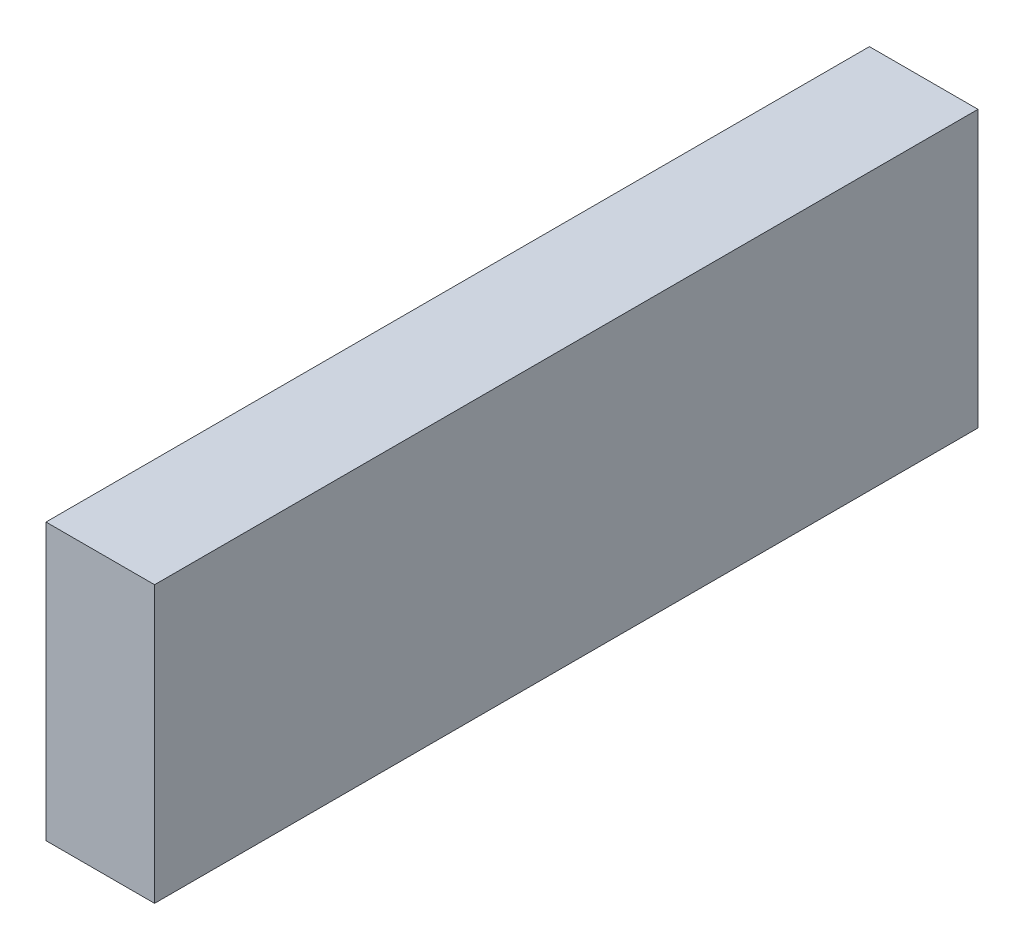
SolidWorks part; units mm, degrees
ref_plane "Front Plane" through (0, 0, 0) normal (0, 0, 1) x (1, 0, 0)
ref_plane "Top Plane" through (0, 0, 0) normal (0, 1, 0) x (1, 0, 0)
ref_plane "Right Plane" through (0, 0, 0) normal (1, 0, 0) x (0, 0, -1)
sketch "Sketch1" plane through (0, 0, 0) normal (0, 1, 0) x (1, 0, 0)
  line L1 (12, -91) -> (-12, -91)
  line L2 (12, -91) -> (12, 91)
  line L3 (12, 91) -> (-12, 91)
  line L4 (-12, -91) -> (-12, 91)
  line L5 (12, -91) -> (-12, 91) construction
  line L6 (12, 91) -> (-12, -91) construction
  point P0 (0, 0)
  dimension "D1" = 24
  dimension "D2" = 182
extrude "Boss-Extrude1" add sketch "Sketch1" along normal blind 61
